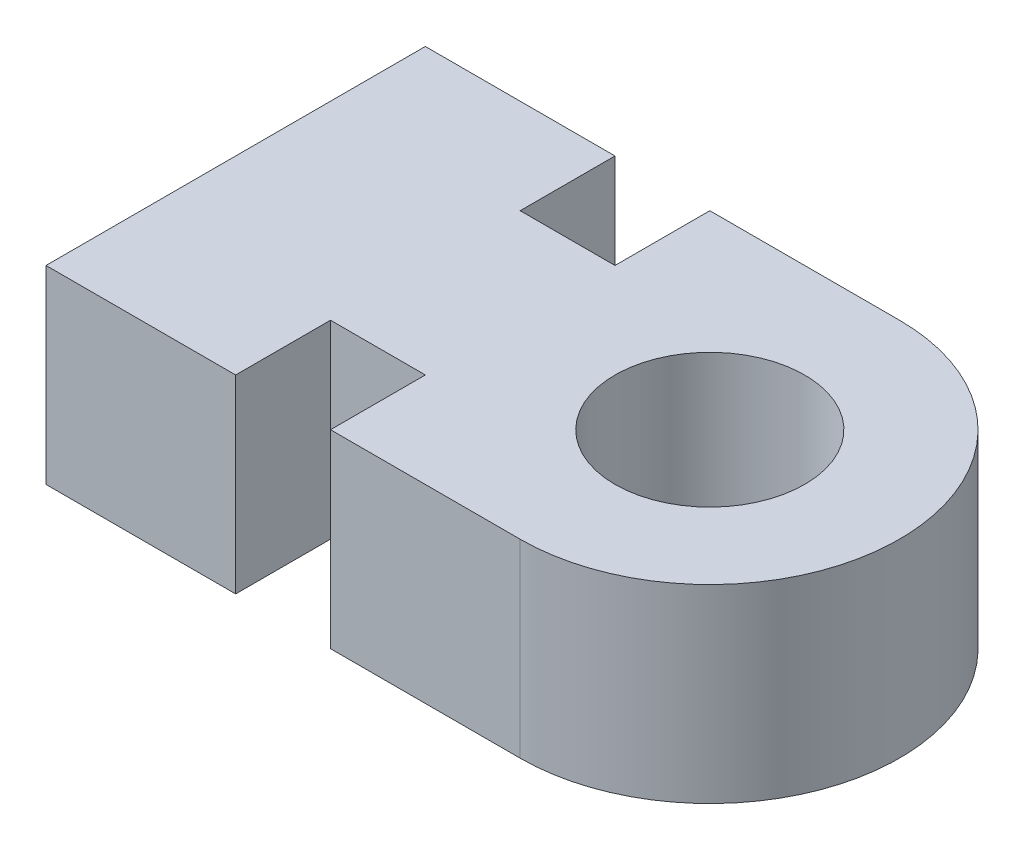
SolidWorks part; units mm, degrees
ref_plane "前基準面" through (0, 0, 0) normal (0, 0, 1) x (1, 0, 0)
ref_plane "上基準面" through (0, 0, 0) normal (0, 1, 0) x (1, 0, 0)
ref_plane "右基準面" through (0, 0, 0) normal (1, 0, 0) x (0, 0, -1)
sketch "草圖1" plane through (0, 0, 0) normal (0, 1, 0) x (1, 0, 0)
  line L0 (0, 0) -> (-16.7995, 0) construction
  line L1 (0, 10) -> (-25, 10)
  line L3 (0, -10) -> (-25, -10)
  line L4 (-25, 10) -> (-25, -10)
  line L5 (-15, 10) -> (-10, 10)
  line L6 (-15, 10) -> (-15, 5)
  line L7 (-15, 5) -> (-10, 5)
  line L8 (-10, 10) -> (-10, 5)
  line L9 (-10, -10) -> (-10, -5)
  line L10 (-15, -10) -> (-15, -5)
  line L11 (-15, -5) -> (-10, -5)
  line L12 (-10, -10) -> (-15, -10)
  circle A0 centre (0, 0) radius 5
  arc A1 (0, -10) -> (0, 10) centre (0, 0) ccw
  dimension "D1" = 20
  dimension "D2" = 10
  dimension "D4" = 5
  dimension "D3" = 25
  dimension "D5" = 5
  dimension "D6" = 10
extrude "填料-伸長1" add sketch "草圖1" along normal blind 10
scale "縮放比例1" scale about centroid uniform scaling yes scale factor 0.2
